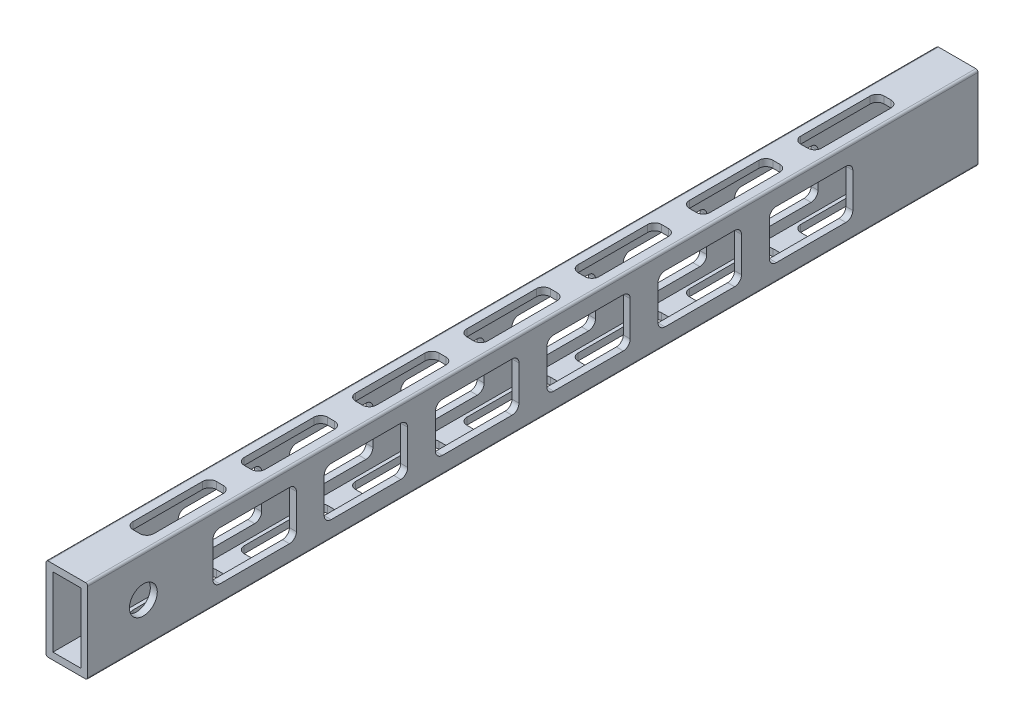
SolidWorks part; units mm, degrees
material "6061-T6 (SS)"
ref_plane "Front Plane" through (0, 0, 0) normal (0, 0, 1) x (1, 0, 0)
ref_plane "Top Plane" through (0, 0, 0) normal (0, 1, 0) x (1, 0, 0)
ref_plane "Right Plane" through (0, 0, 0) normal (1, 0, 0) x (0, 0, -1)
sketch "Sketch1" plane through (0, 0, 0) normal (0, 0, 1) x (1, 0, 0)
  line L0 (-6.35, -15.875) -> (-6.35, 15.875)
  line L1 (-8.525, -19.05) -> (8.525, -19.05)
  line L2 (-9.525, -18.05) -> (-9.525, 18.05)
  line L3 (-8.525, 19.05) -> (8.525, 19.05)
  line L4 (9.525, -18.05) -> (9.525, 18.05)
  line L5 (-9.525, -19.05) -> (9.525, 19.05) construction
  line L6 (-9.525, 19.05) -> (9.525, -19.05) construction
  line L7 (-6.35, 15.875) -> (6.35, 15.875)
  line L8 (6.35, -15.875) -> (6.35, 15.875)
  line L9 (-6.35, -15.875) -> (6.35, -15.875)
  arc A0 (-8.525, -19.05) -> (-9.525, -18.05) centre (-8.525, -18.05) cw
  arc A1 (8.525, -19.05) -> (9.525, -18.05) centre (8.525, -18.05) ccw
  arc A2 (8.525, 19.05) -> (9.525, 18.05) centre (8.525, 18.05) cw
  arc A3 (-9.525, 18.05) -> (-8.525, 19.05) centre (-8.525, 18.05) cw
  arc A4 (-6.35, 15.875) -> (-6.35, 15.875) centre (-6.35, 15.875) cw
  arc A5 (6.35, 15.875) -> (6.35, 15.875) centre (6.35, 15.875) cw
  arc A6 (6.35, -15.875) -> (6.35, -15.875) centre (6.35, -15.875) ccw
  arc A7 (-6.35, -15.875) -> (-6.35, -15.875) centre (-6.35, -15.875) cw
  point P0 (0, 0)
  dimension "D3" = 1
  dimension "D1" = 19.05
  dimension "D2" = 38.1
  dimension "D4" = 3.175
extrude "Boss-Extrude1" add sketch "Sketch1" along normal mid plane 406.4
sketch "Sketch2" plane through (0, 19.05, 0) normal (0, 1, 0) x (1, 0, 0)
  line L0 (-4.7625, -117.475) -> (-4.7625, -85.725)
  line L1 (-1.5875, -171.45) -> (1.5875, -171.45)
  line L2 (-4.7625, -168.275) -> (-4.7625, -136.525)
  line L3 (-1.5875, -133.35) -> (1.5875, -133.35)
  line L4 (4.7625, -168.275) -> (4.7625, -136.525)
  line L5 (-4.7625, -171.45) -> (4.7625, -133.35) construction
  line L6 (-4.7625, -133.35) -> (4.7625, -171.45) construction
  line L7 (-1.5875, -120.65) -> (1.5875, -120.65)
  line L8 (4.7625, -117.475) -> (4.7625, -85.725)
  line L9 (-1.5875, -82.55) -> (1.5875, -82.55)
  line L10 (-4.7625, -66.675) -> (-4.7625, -34.925)
  line L11 (-1.5875, -69.85) -> (1.5875, -69.85)
  line L12 (4.7625, -66.675) -> (4.7625, -34.925)
  line L13 (-1.5875, -31.75) -> (1.5875, -31.75)
  line L14 (-4.7625, -15.875) -> (-4.7625, 15.875)
  line L15 (-1.5875, -19.05) -> (1.5875, -19.05)
  line L16 (4.7625, -15.875) -> (4.7625, 15.875)
  line L17 (-1.5875, 19.05) -> (1.5875, 19.05)
  line L18 (-4.7625, 34.925) -> (-4.7625, 66.675)
  line L19 (-1.5875, 31.75) -> (1.5875, 31.75)
  line L20 (4.7625, 34.925) -> (4.7625, 66.675)
  line L21 (-1.5875, 69.85) -> (1.5875, 69.85)
  line L22 (0, -152.4) -> (0, -101.6) construction
  line L23 (-4.7625, 85.725) -> (-4.7625, 117.475)
  line L24 (-1.5875, 82.55) -> (1.5875, 82.55)
  line L25 (4.7625, 85.725) -> (4.7625, 117.475)
  line L26 (-1.5875, 120.65) -> (1.5875, 120.65)
  line L27 (-4.7625, 136.525) -> (-4.7625, 168.275)
  line L28 (-1.5875, 133.35) -> (1.5875, 133.35)
  line L29 (4.7625, 136.525) -> (4.7625, 168.275)
  line L30 (-1.5875, 171.45) -> (1.5875, 171.45)
  arc A0 (-1.5875, -171.45) -> (-4.7625, -168.275) centre (-1.5875, -168.275) cw
  arc A1 (1.5875, -171.45) -> (4.7625, -168.275) centre (1.5875, -168.275) ccw
  arc A2 (1.5875, -133.35) -> (4.7625, -136.525) centre (1.5875, -136.525) cw
  arc A3 (-4.7625, -136.525) -> (-1.5875, -133.35) centre (-1.5875, -136.525) cw
  arc A4 (-4.7625, -85.725) -> (-1.5875, -82.55) centre (-1.5875, -85.725) cw
  arc A5 (-1.5875, -120.65) -> (-4.7625, -117.475) centre (-1.5875, -117.475) cw
  arc A6 (1.5875, -120.65) -> (4.7625, -117.475) centre (1.5875, -117.475) ccw
  arc A7 (1.5875, -82.55) -> (4.7625, -85.725) centre (1.5875, -85.725) cw
  arc A8 (-4.7625, -34.925) -> (-1.5875, -31.75) centre (-1.5875, -34.925) cw
  arc A9 (-1.5875, -69.85) -> (-4.7625, -66.675) centre (-1.5875, -66.675) cw
  arc A10 (1.5875, -69.85) -> (4.7625, -66.675) centre (1.5875, -66.675) ccw
  arc A11 (1.5875, -31.75) -> (4.7625, -34.925) centre (1.5875, -34.925) cw
  arc A12 (-4.7625, 15.875) -> (-1.5875, 19.05) centre (-1.5875, 15.875) cw
  arc A13 (-1.5875, -19.05) -> (-4.7625, -15.875) centre (-1.5875, -15.875) cw
  arc A14 (1.5875, -19.05) -> (4.7625, -15.875) centre (1.5875, -15.875) ccw
  arc A15 (1.5875, 19.05) -> (4.7625, 15.875) centre (1.5875, 15.875) cw
  arc A16 (-4.7625, 66.675) -> (-1.5875, 69.85) centre (-1.5875, 66.675) cw
  arc A17 (-1.5875, 31.75) -> (-4.7625, 34.925) centre (-1.5875, 34.925) cw
  arc A18 (1.5875, 31.75) -> (4.7625, 34.925) centre (1.5875, 34.925) ccw
  arc A19 (1.5875, 69.85) -> (4.7625, 66.675) centre (1.5875, 66.675) cw
  arc A20 (-4.7625, 117.475) -> (-1.5875, 120.65) centre (-1.5875, 117.475) cw
  arc A21 (-1.5875, 82.55) -> (-4.7625, 85.725) centre (-1.5875, 85.725) cw
  arc A22 (1.5875, 82.55) -> (4.7625, 85.725) centre (1.5875, 85.725) ccw
  arc A23 (1.5875, 120.65) -> (4.7625, 117.475) centre (1.5875, 117.475) cw
  arc A24 (-4.7625, 168.275) -> (-1.5875, 171.45) centre (-1.5875, 168.275) cw
  arc A25 (-1.5875, 133.35) -> (-4.7625, 136.525) centre (-1.5875, 136.525) cw
  arc A26 (1.5875, 133.35) -> (4.7625, 136.525) centre (1.5875, 136.525) ccw
  arc A27 (1.5875, 171.45) -> (4.7625, 168.275) centre (1.5875, 168.275) cw
  point P0 (0, -152.4)
  point P19 (0, 101.6)
  point P20 (0, -101.6)
  point P33 (0, -50.8)
  point P46 (0, 0)
  point P59 (0, 50.8)
  point P86 (0, 152.4)
  dimension "D3" = 3.175
  dimension "D1" = 9.525
  dimension "D2" = 38.1
  dimension "D5" = 50.8
  dimension "D4" = 7
extrude "Cut-Extrude1" cut sketch "Sketch2" against normal through all both and the other way through all
sketch "Sketch3" plane through (9.525, 0, 0) normal (1, 0, 0) x (0, 0, -1)
  line L0 (-95.25, -7.9375) -> (-95.25, 7.9375)
  line L1 (-142.875, -11.1125) -> (-111.125, -11.1125)
  line L2 (-146.05, -7.9375) -> (-146.05, 7.9375)
  line L3 (-142.875, 11.1125) -> (-111.125, 11.1125)
  line L4 (-107.95, -7.9375) -> (-107.95, 7.9375)
  line L5 (-146.05, -11.1125) -> (-107.95, 11.1125) construction
  line L6 (-146.05, 11.1125) -> (-107.95, -11.1125) construction
  line L7 (-92.075, -11.1125) -> (-60.325, -11.1125)
  line L8 (-57.15, -7.9375) -> (-57.15, 7.9375)
  line L9 (-92.075, 11.1125) -> (-60.325, 11.1125)
  line L10 (-44.45, -7.9375) -> (-44.45, 7.9375)
  line L11 (-41.275, -11.1125) -> (-9.525, -11.1125)
  line L12 (-6.35, -7.9375) -> (-6.35, 7.9375)
  line L13 (-41.275, 11.1125) -> (-9.525, 11.1125)
  line L14 (-127, 0) -> (-76.2, 0) construction
  line L15 (6.35, -7.9375) -> (6.35, 7.9375)
  line L16 (9.525, -11.1125) -> (41.275, -11.1125)
  line L17 (44.45, -7.9375) -> (44.45, 7.9375)
  line L18 (9.525, 11.1125) -> (41.275, 11.1125)
  line L19 (-25.4, 0) -> (25.4, 0) construction
  line L20 (57.15, -7.9375) -> (57.15, 7.9375)
  line L21 (60.325, -11.1125) -> (92.075, -11.1125)
  line L22 (95.25, -7.9375) -> (95.25, 7.9375)
  line L23 (60.325, 11.1125) -> (92.075, 11.1125)
  line L24 (107.95, -7.9375) -> (107.95, 7.9375)
  line L25 (111.125, -11.1125) -> (142.875, -11.1125)
  line L26 (146.05, -7.9375) -> (146.05, 7.9375)
  line L27 (111.125, 11.1125) -> (142.875, 11.1125)
  arc A0 (-142.875, -11.1125) -> (-146.05, -7.9375) centre (-142.875, -7.9375) cw
  arc A1 (-111.125, -11.1125) -> (-107.95, -7.9375) centre (-111.125, -7.9375) ccw
  arc A2 (-111.125, 11.1125) -> (-107.95, 7.9375) centre (-111.125, 7.9375) cw
  arc A3 (-146.05, 7.9375) -> (-142.875, 11.1125) centre (-142.875, 7.9375) cw
  arc A4 (-95.25, 7.9375) -> (-92.075, 11.1125) centre (-92.075, 7.9375) cw
  arc A5 (-92.075, -11.1125) -> (-95.25, -7.9375) centre (-92.075, -7.9375) cw
  arc A6 (-60.325, -11.1125) -> (-57.15, -7.9375) centre (-60.325, -7.9375) ccw
  arc A7 (-60.325, 11.1125) -> (-57.15, 7.9375) centre (-60.325, 7.9375) cw
  arc A8 (-44.45, 7.9375) -> (-41.275, 11.1125) centre (-41.275, 7.9375) cw
  arc A9 (-41.275, -11.1125) -> (-44.45, -7.9375) centre (-41.275, -7.9375) cw
  arc A10 (-9.525, -11.1125) -> (-6.35, -7.9375) centre (-9.525, -7.9375) ccw
  arc A11 (-9.525, 11.1125) -> (-6.35, 7.9375) centre (-9.525, 7.9375) cw
  arc A12 (6.35, 7.9375) -> (9.525, 11.1125) centre (9.525, 7.9375) cw
  arc A13 (9.525, -11.1125) -> (6.35, -7.9375) centre (9.525, -7.9375) cw
  arc A14 (41.275, -11.1125) -> (44.45, -7.9375) centre (41.275, -7.9375) ccw
  arc A15 (41.275, 11.1125) -> (44.45, 7.9375) centre (41.275, 7.9375) cw
  arc A16 (57.15, 7.9375) -> (60.325, 11.1125) centre (60.325, 7.9375) cw
  arc A17 (60.325, -11.1125) -> (57.15, -7.9375) centre (60.325, -7.9375) cw
  arc A18 (92.075, -11.1125) -> (95.25, -7.9375) centre (92.075, -7.9375) ccw
  arc A19 (92.075, 11.1125) -> (95.25, 7.9375) centre (92.075, 7.9375) cw
  arc A20 (107.95, 7.9375) -> (111.125, 11.1125) centre (111.125, 7.9375) cw
  arc A21 (111.125, -11.1125) -> (107.95, -7.9375) centre (111.125, -7.9375) cw
  arc A22 (142.875, -11.1125) -> (146.05, -7.9375) centre (142.875, -7.9375) ccw
  arc A23 (142.875, 11.1125) -> (146.05, 7.9375) centre (142.875, 7.9375) cw
  point P0 (-127, 0)
  point P19 (25.4, 0)
  point P20 (-76.2, 0)
  point P33 (-25.4, 0)
  point P60 (76.2, 0)
  point P74 (127, 0)
  point P87 (0, 0)
  dimension "D3" = 3.175
  dimension "D1" = 22.225
  dimension "D2" = 38.1
  dimension "D5" = 50.8
  dimension "D4" = 6
extrude "Cut-Extrude2" cut sketch "Sketch3" against normal through all both and the other way through all
sketch "Sketch4" plane through (9.525, 0, 0) normal (1, 0, 0) x (0, 0, -1)
  line L0 (-203.2, 19.05) -> (203.2, 19.05) construction
  line L1 (-203.2, -18.05) -> (-203.2, 18.05) construction
  circle A0 centre (-177.8, 0) radius 6.35
  point P2 (-177.0845, 5.1185)
  dimension "D1" = 12.7
  dimension "D2" = 19.05
  dimension "D3" = 25.4
extrude "Cut-Extrude3" cut sketch "Sketch4" against normal through all both and the other way through all
